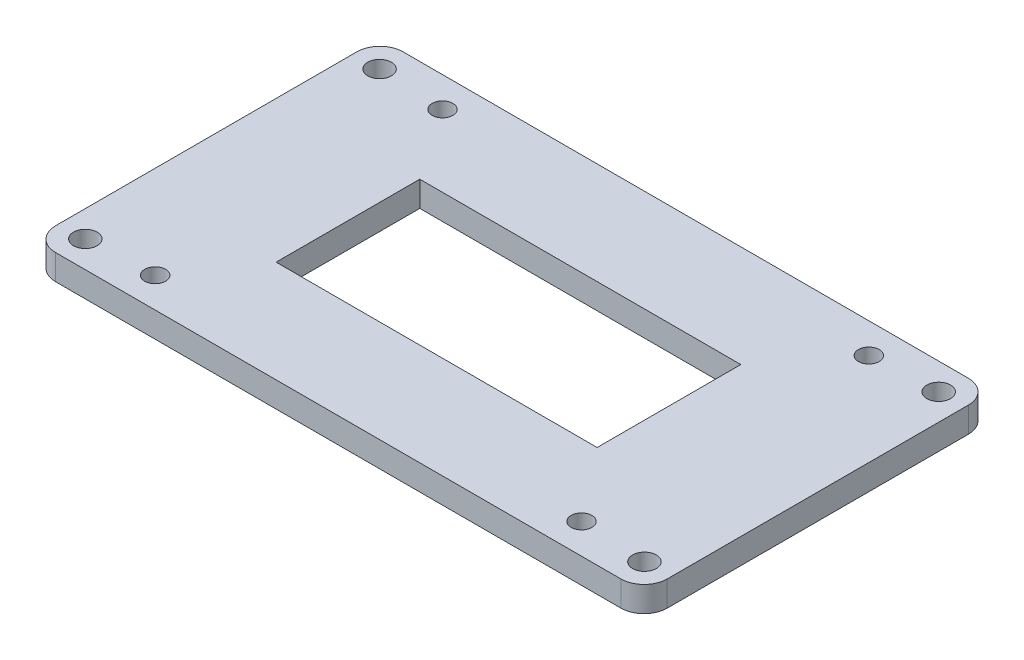
SolidWorks part; units mm, degrees
ref_plane "Front Plane" through (0, 0, 0) normal (0, 0, 1) x (1, 0, 0)
ref_plane "Top Plane" through (0, 0, 0) normal (0, 1, 0) x (1, 0, 0)
ref_plane "Right Plane" through (0, 0, 0) normal (1, 0, 0) x (0, 0, -1)
sketch "Sketch2" plane through (0, 0, 0) normal (0, 1, 0) x (1, 0, 0)
  line L1 (-66, 37.5) -> (66, 37.5)
  line L2 (-66, 37.5) -> (-66, -37.5)
  line L3 (-66, -37.5) -> (66, -37.5)
  line L4 (66, 37.5) -> (66, -37.5)
  line L5 (-66, 37.5) -> (66, -37.5) construction
  line L6 (-66, -37.5) -> (66, 37.5) construction
  point P0 (0, 0)
  dimension "D1" = 75
  dimension "D2" = 132
extrude "Boss-Extrude1" add sketch "Sketch2" along normal blind 5.461
hole_wizard "#8 Clearance Hole1" positions "Sketch3" profile "Sketch4" hole size "#8" standard "ANSI Inch" end condition through all
sketch "Sketch3" plane through (0, 5.461, 0) normal (0, 1, 0) x (1, 0, 0)
  line L1 (-46, 31) -> (46, 31)
  line L2 (-46, 31) -> (-46, -31)
  line L3 (-46, -31) -> (46, -31)
  line L4 (46, 31) -> (46, -31)
  line L5 (-46, 31) -> (46, -31) construction
  line L6 (-46, -31) -> (46, 31) construction
  point P2 (46, -31)
  point P23 (-46, 31)
  point P24 (-46, -31)
  point P25 (46, 31)
  dimension "D1" = 92
  dimension "D2" = 62
sketch "Sketch4" plane through (46, 5.461, 31) normal (1, 0, 0) x (0, 0, 1)
  line L0 (0, 0) -> (0, 5.461)
  line L1 (0, 5.461) -> (2.2479, 5.461)
  line L2 (2.2479, 5.461) -> (2.2479, 0)
  line L5 (2.2479, 0) -> (0, 0)
  line L11 (0, -6.35) -> (0, 107.95) construction
  dimension "Thru Hole Dia." = 4.4958
  dimension "Thru Hole Depth" = 5.461
hole_wizard "#10 Clearance Hole1" positions "Sketch5" profile "Sketch6" hole size "#10" standard "ANSI Inch" end condition through all
sketch "Sketch5" plane through (0, 5.461, 0) normal (0, 1, 0) x (1, 0, 0)
  line L1 (-60.325, 31.75) -> (60.325, 31.75)
  line L2 (-60.325, 31.75) -> (-60.325, -31.75)
  line L3 (-60.325, -31.75) -> (60.325, -31.75)
  line L4 (60.325, 31.75) -> (60.325, -31.75)
  line L5 (-60.325, 31.75) -> (60.325, -31.75) construction
  line L6 (-60.325, -31.75) -> (60.325, 31.75) construction
  point P2 (60.325, -31.75)
  point P39 (-60.325, 31.75)
  point P40 (-60.325, -31.75)
  point P41 (60.325, 31.75)
  dimension "D1" = 63.5
  dimension "D2" = 120.65
sketch "Sketch6" plane through (60.325, 5.461, 31.75) normal (1, 0, 0) x (0, 0, 1)
  line L0 (0, 0) -> (0, 5.461)
  line L1 (0, 5.461) -> (2.5527, 5.461)
  line L2 (2.5527, 5.461) -> (2.5527, 0)
  line L5 (2.5527, 0) -> (0, 0)
  line L11 (0, -6.35) -> (0, 107.95) construction
  dimension "Thru Hole Dia." = 5.1054
  dimension "Thru Hole Depth" = 5.461
fillet "Fillet1" radius 5 4 edges at (66, 2.7305, 37.5) (66, 2.7305, -37.5) (-66, 2.7305, 37.5) (-66, 2.7305, -37.5)
sketch "Sketch7" plane through (0, 5.461, 0) normal (0, 1, 0) x (1, 0, 0)
  line L1 (-35.4, 15.5) -> (33.87, 15.5)
  line L2 (-35.4, 15.5) -> (-35.4, -15.5)
  line L3 (-35.4, -15.5) -> (33.87, -15.5)
  line L4 (33.87, 15.5) -> (33.87, -15.5)
  line L5 (-35.4, 15.5) -> (33.87, -15.5) construction
  line L6 (-35.4, -15.5) -> (33.87, 15.5) construction
  circle A0 centre (46, -31) radius 2.2479 construction
  circle A1 centre (-46, -31) radius 2.2479 construction
  point P0 (-0.765, 0)
  point P9 (0, 0)
  dimension "D2" = 10.6
  dimension "D1" = 12.13
  dimension "D3" = 31
extrude "Cut-Extrude1" cut sketch "Sketch7" against normal through all
equation "\"D2@Sketch2\"=110+11*2"
equation "\"D1@Sketch5\"=2.5in"
equation "\"D2@Sketch5\"=4.75in"
